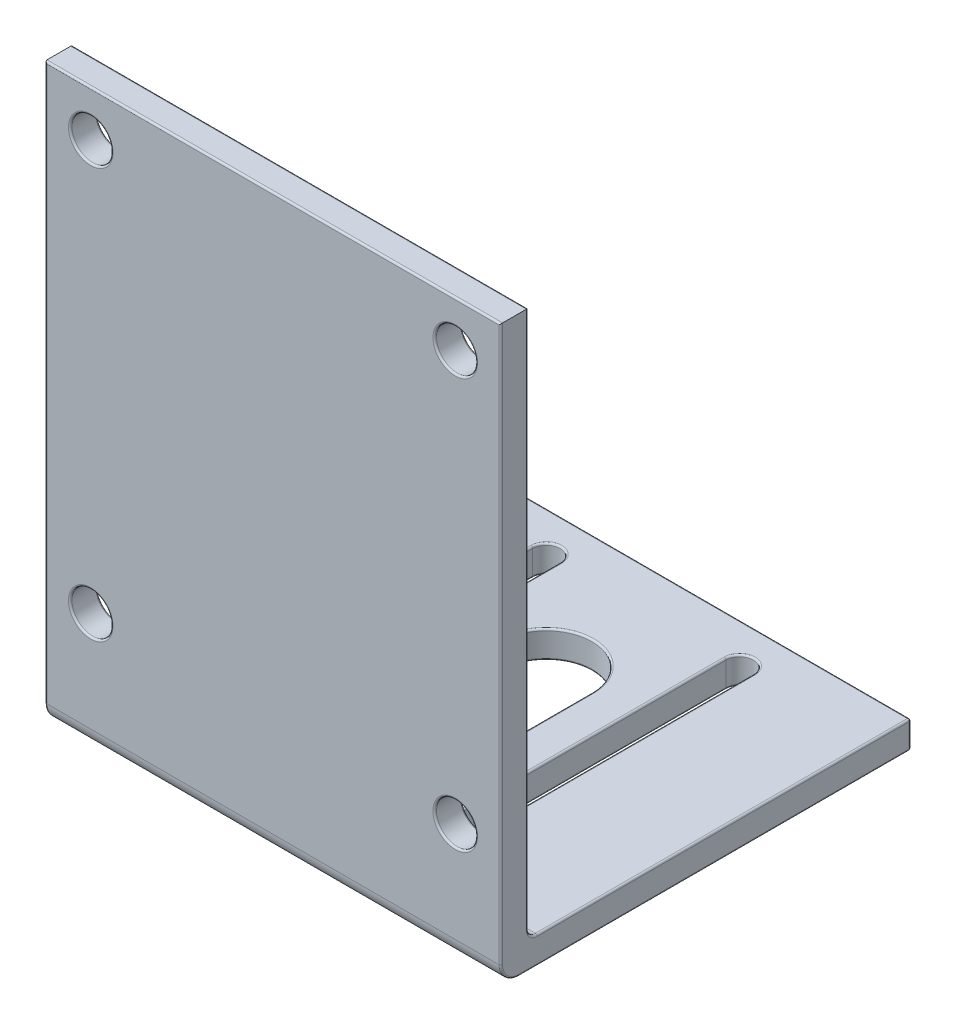
SolidWorks part; units mm, degrees
ref_plane "Front Plane" through (0, 0, 0) normal (0, 0, 1) x (1, 0, 0)
ref_plane "Top Plane" through (0, 0, 0) normal (0, 1, 0) x (1, 0, 0)
ref_plane "Right Plane" through (0, 0, 0) normal (1, 0, 0) x (0, 0, -1)
sketch "Sketch1" plane through (0, 0, 0) normal (0, 1, 0) x (1, 0, 0)
  line L0 (-10.6082, 20.605) -> (-10.6082, -10.605) construction
  line L5 (-10.6082, -10.605) -> (10.6082, 10.605) construction
  line L6 (-10.6082, 10.605) -> (10.6082, -10.605) construction
  line L7 (-25, 20) -> (25, 20)
  line L8 (-25, 20) -> (-25, -20)
  line L9 (-25, -20) -> (25, -20)
  line L10 (25, 20) -> (25, -20)
  line L11 (0, 10) -> (0, 0) construction
  line L12 (5, 10) -> (5, 0)
  line L13 (-9.1082, 20.605) -> (-9.1082, -10.605)
  line L14 (-12.1082, 20.605) -> (-12.1082, -10.605)
  line L15 (0, 20) -> (0, 0) construction
  line L16 (10.6082, 20.605) -> (10.6082, -10.605) construction
  line L17 (9.1082, 20.605) -> (9.1082, -10.605)
  line L18 (12.1082, 20.605) -> (12.1082, -10.605)
  line L19 (-5, 10) -> (-5, 0)
  line L20 (-25, 20) -> (25, 20)
  line L21 (-25, 20) -> (-25, 25)
  line L22 (-25, 25) -> (25, 25)
  line L23 (25, 20) -> (25, 25)
  circle A0 centre (0, 0) radius 15 construction
  circle A1 centre (0, 0) radius 11 construction
  circle A2 centre (-10.6082, 10.605) radius 1.5 construction
  circle A3 centre (10.6082, 10.605) radius 1.5 construction
  circle A4 centre (-10.6082, -10.605) radius 1.5 construction
  circle A5 centre (10.6082, -10.605) radius 1.5 construction
  circle A6 centre (0, 0) radius 5 construction
  arc A7 (-9.1082, 20.605) -> (-12.1082, 20.605) centre (-10.6082, 20.605) ccw
  arc A8 (-12.1082, -10.605) -> (-9.1082, -10.605) centre (-10.6082, -10.605) ccw
  arc A9 (9.1082, 20.605) -> (12.1082, 20.605) centre (10.6082, 20.605) cw
  arc A10 (12.1082, -10.605) -> (9.1082, -10.605) centre (10.6082, -10.605) cw
  arc A11 (5, 10) -> (-5, 10) centre (0, 10) ccw
  arc A12 (-5, 0) -> (5, 0) centre (0, 0) ccw
  point P17 (-10.6082, 20.605)
  point P19 (-10.6082, 5)
  point P26 (10.6082, 5)
  point P33 (0, 10)
  point P35 (0, 5)
  dimension "D1" = 30
  dimension "D4" = 22
  dimension "D5" = 10
  dimension "D9" = 1.5
  dimension "D12" = 5
  dimension "D2" = 21.21
  dimension "D3" = 21.2164
  dimension "D6" = 40
  dimension "D7" = 50
  dimension "D8" = 10
  dimension "D10" = 5
  dimension "D11" = 10
extrude "Boss-Extrude1" add sketch "Sketch1" along normal blind 3 contours L18 A10 L17 L7 L13 A8 L14 L8 L9 L10 | L17 A9 L18 L7 L23 L22 L21 L14 A7 L13
sketch "Sketch2" plane through (0, 3, 0) normal (0, 1, 0) x (1, 0, 0)
  line L0 (25, 25) -> (25, -20) construction
  line L1 (-25, -20) -> (25, -20)
  line L2 (-25, -20) -> (-25, -17)
  line L3 (-25, -17) -> (25, -17)
  line L4 (25, -20) -> (25, -17)
  dimension "D1" = 3
extrude "Boss-Extrude2" add sketch "Sketch2" along normal blind 60
sketch "Sketch3" plane through (0, 0, 17) normal (0, 0, -1) x (-1, 0, 0)
  line L0 (20, 8) -> (20, 58) construction
  line L1 (25, 3) -> (-25, 3) construction
  line L2 (25, 3) -> (25, 63) construction
  line L3 (25, 63) -> (-25, 63) construction
  line L4 (-25, 3) -> (-25, 63) construction
  line L5 (20, 58) -> (-20, 58) construction
  line L6 (-20, 8) -> (-20, 58) construction
  line L7 (20, 8) -> (-20, 8) construction
  line L8 (-20, 13) -> (20, 13) construction
  circle A0 centre (20, 58) radius 2.25
  circle A1 centre (-20, 58) radius 2.25
  circle A4 centre (-20, 13) radius 2.25
  circle A5 centre (20, 13) radius 2.25
  point P14 (-20, 13)
  dimension "D2" = 5
  dimension "D3" = 4.5
  dimension "D1" = 5
extrude "Cut-Extrude1" cut sketch "Sketch3" against normal blind 60
fillet "Fillet1" radius 1 1 edges at (0, 3, 17)
fillet "Fillet2" radius 2 1 edges at (0, 0, 20)
fillet "Fillet3" radius 0.2 50 edges at (-25, 0.5858, 19.4142) (25, 0.5858, 19.4142) (-25, 3.2929, 16.7071) (25, 3.2929, 16.7071) (0, 63, 20) (25, 32.5, 20) (-25, 32.5, 20) (-22.25, 58, 20) (17.75, 58, 20) (-25, 0, -3.5) (25, 0, -3.5) (-5, 0, -5) (0, 0, -15) (5, 0, -5) (0, 0, 5) (-10.6082, 0, -22.105) (-9.1082, 0, -5) (-10.6082, 0, 12.105) (-12.1082, 0, -5) (10.6082, 0, -22.105) (12.1082, 0, -5) (10.6082, 0, 12.105) (9.1082, 0, -5) (5, 3, -5) (0, 3, -15) (-5, 3, -5) (0, 3, 5) (-10.6082, 3, 12.105) (-9.1082, 3, -5) (-10.6082, 3, -22.105) (-12.1082, 3, -5) (10.6082, 3, 12.105) (12.1082, 3, -5) (10.6082, 3, -22.105) (9.1082, 3, -5) (25, 3, -4.5) (-25, 3, -4.5) (25, 1.5, -25) (0, 3, -25) (-25, 1.5, -25) (0, 0, -25) (0, 63, 17) (-25, 33.5, 17) (25, 33.5, 17) (-22.25, 58, 17) (17.75, 58, 17) (17.75, 13, 20) (-22.25, 13, 20) (17.75, 13, 17) (-22.25, 13, 17)
